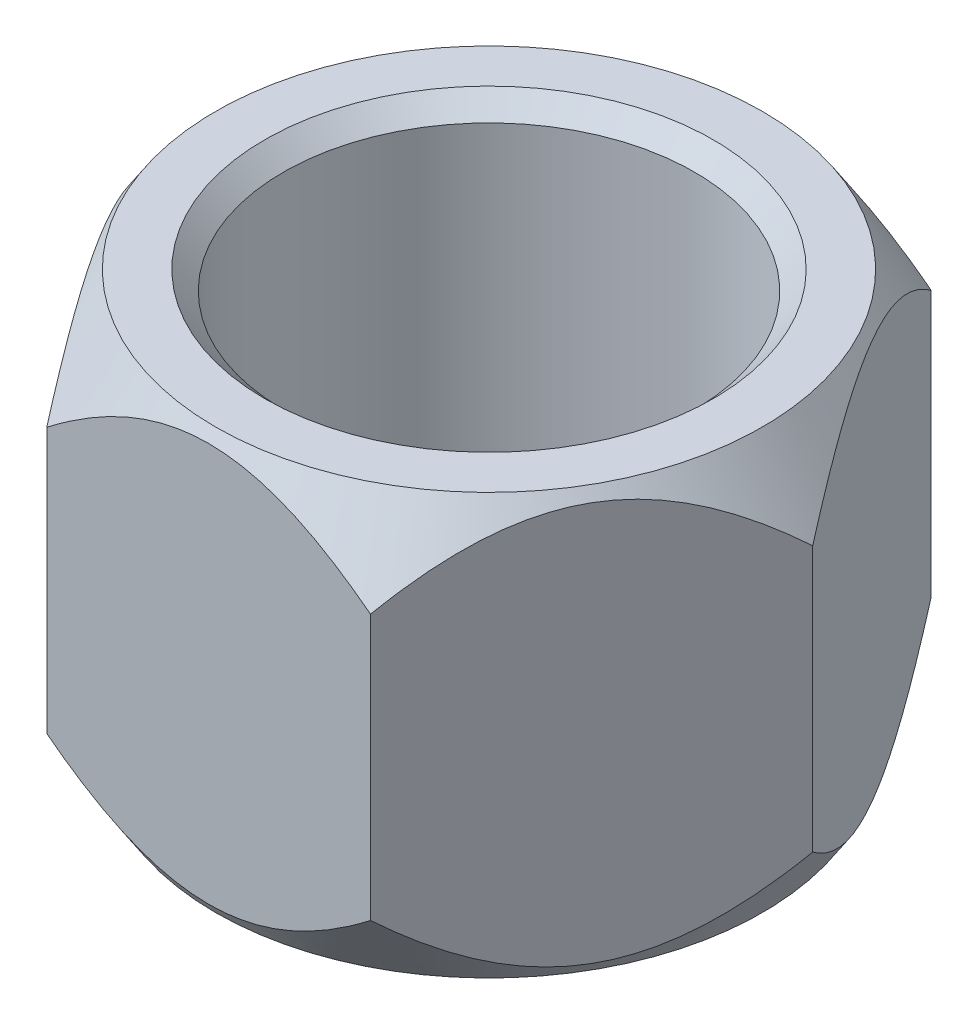
SolidWorks part; units mm, degrees
ref_plane "Спереди" through (0, 0, 0) normal (0, 0, 1) x (1, 0, 0)
ref_plane "Сверху" through (0, 0, 0) normal (0, 1, 0) x (1, 0, 0)
ref_plane "Справа" through (0, 0, 0) normal (1, 0, 0) x (0, 0, -1)
sketch "Эскиз1" plane through (0, 0, 0) normal (0, 1, 0) x (1, 0, 0)
  line L1 (17.3205, 0) -> (8.6603, 15)
  line L2 (8.6603, 15) -> (-8.6603, 15)
  line L3 (-8.6603, 15) -> (-17.3205, 0)
  line L4 (-17.3205, 0) -> (-8.6603, -15)
  line L5 (-8.6603, -15) -> (8.6603, -15)
  line L6 (8.6603, -15) -> (17.3205, 0)
  circle A1 centre (0, 0) radius 15 construction
  dimension "D1" = 30
extrude "Бобышка-Вытянуть1" add sketch "Эскиз1" along normal blind 22.5
sketch "Эскиз2" plane through (0, 22.5, 0) normal (0, 1, 0) x (1, 0, 0)
  circle A0 centre (0, 0) radius 11
  dimension "D1" = 22
extrude "Вырез-Вытянуть2" cut sketch "Эскиз2" against normal blind 18
cosmetic thread "Условное изображение резьбы2" parameters "D2"=24
sketch "Эскиз3" plane through (0, 0, 0) normal (0, -1, 0) x (1, 0, 0)
  circle A0 centre (0, 0) radius 4
  dimension "D1" = 8
extrude "Вырез-Вытянуть3" cut sketch "Эскиз3" against normal up to next
ref_plane "Плоскость1" through (0, 0, 0) normal (-0.866, 0, -0.5) x (-0.5, 0, 0.866)
sketch "Эскиз4" plane through (0, 0, 0) normal (-0.866, 0, -0.5) x (-0.5, 0, 0.866)
  line L0 (-17.3205, 18.3458) -> (-17.3205, 22.5)
  line L1 (-17.3205, 22.5) -> (-17.3205, 0) construction
  line L2 (-17.3205, 22.5) -> (-14.6283, 22.5)
  line L3 (-17.3205, 22.5) -> (-8.6603, 22.5) construction
  line L4 (-14.6283, 22.5) -> (-17.3205, 18.3458)
  line L5 (0, 0) -> (0, 26.4787) construction
revolve "Вырез-Повернуть1" cut sketch "Эскиз4" angle 360 about L5
ref_plane "Плоскость2" through (0, 11.25, 0) normal (0, 1, 0) x (1, 0, 0)
mirror "Зеркальное отражение1" about plane through (0, 11.25, 0) normal (0, 1, 0) of "Вырез-Повернуть1"
chamfer "Фаска1" distance 1 angle 45 1 edges at (0, 22.5, 11)
